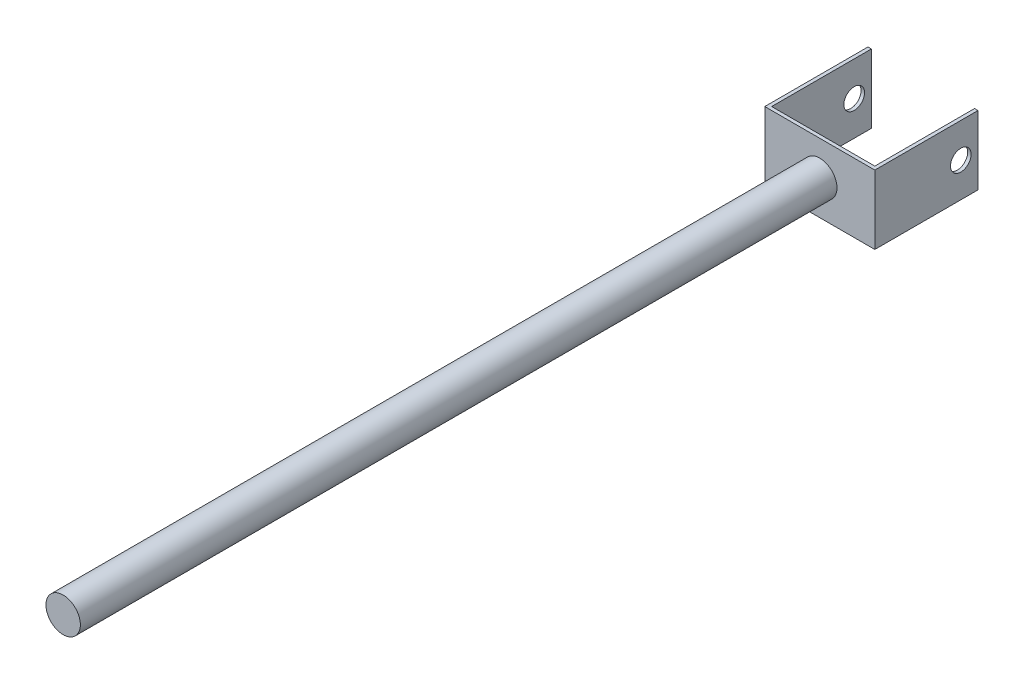
SolidWorks part; units mm, degrees
ref_plane "Front Plane" through (0, 0, 0) normal (0, 0, 1) x (1, 0, 0)
ref_plane "Top Plane" through (0, 0, 0) normal (0, 1, 0) x (1, 0, 0)
ref_plane "Right Plane" through (0, 0, 0) normal (1, 0, 0) x (0, 0, -1)
sketch "Sketch1" plane through (0, 0, 0) normal (0, 1, 0) x (1, 0, 0)
  line L0 (0, 0) -> (-80, 0)
  line L1 (-80, 0) -> (-80, 150)
  line L2 (-80, 150) -> (-75, 150)
  line L3 (-75, 150) -> (-75, 5)
  line L4 (-75, 5) -> (75, 5)
  line L5 (75, 5) -> (75, 150)
  line L6 (75, 150) -> (80, 150)
  line L7 (80, 150) -> (80, 0)
  line L8 (80, 0) -> (0, 0)
  dimension "D1" = 80
  dimension "D2" = 160
  dimension "D3" = 5
  dimension "D4" = 5
  dimension "D5" = 150
  dimension "D6" = 150
  dimension "D7" = 5
extrude "Boss-Extrude1" add sketch "Sketch1" along normal mid plane 100
sketch "Sketch2" plane through (0, 0, 0) normal (0, 0, 1) x (1, 0, 0)
  circle A0 centre (0, 0) radius 25
  dimension "D1" = 50
extrude "Boss-Extrude2" add sketch "Sketch2" along normal blind 1100
sketch "Sketch3" plane through (80, 0, 0) normal (1, 0, 0) x (0, 0, -1)
  line L0 (0, 0) -> (150, 0) construction
  line L1 (150, 50) -> (150, -50) construction
  circle A0 centre (125, 0) radius 15
  dimension "D1" = 30
  dimension "D2" = 125
extrude "Cut-Extrude1" cut sketch "Sketch3" against normal through all
